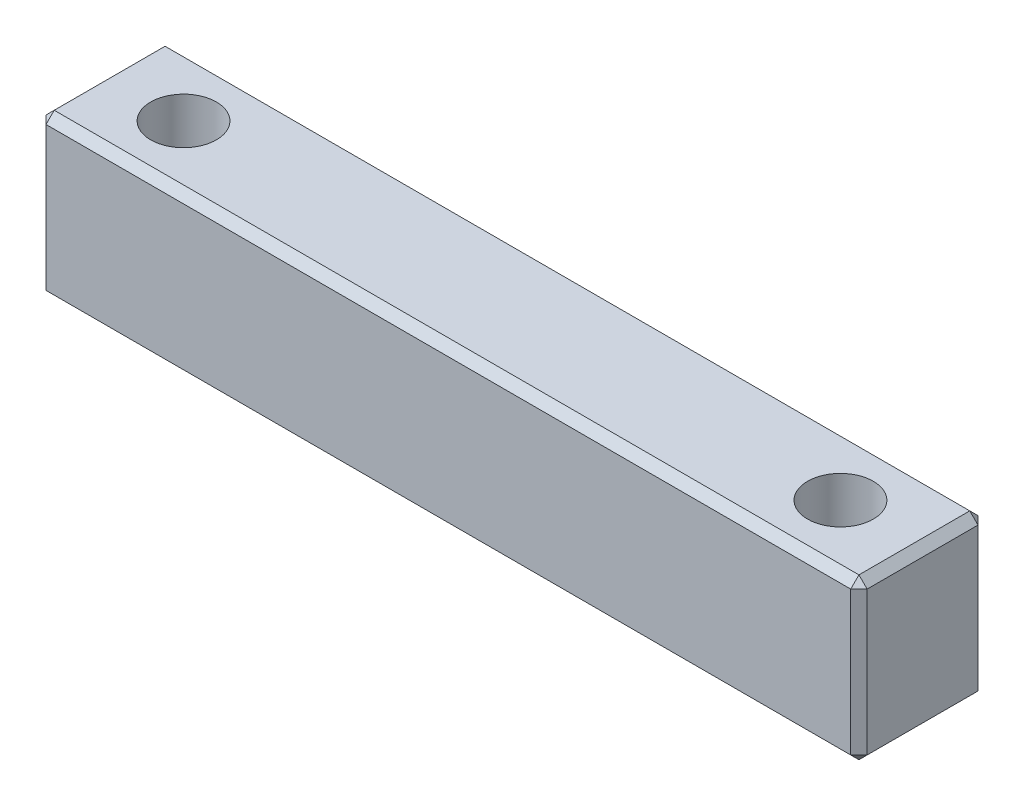
SolidWorks part; units mm, degrees
ref_plane "Front Plane" through (0, 0, 0) normal (0, 0, 1) x (1, 0, 0)
ref_plane "Top Plane" through (0, 0, 0) normal (0, 1, 0) x (1, 0, 0)
ref_plane "Right Plane" through (0, 0, 0) normal (1, 0, 0) x (0, 0, -1)
sketch "Sketch1" plane through (0, 0, 0) normal (1, 0, 0) x (0, 0, -1)
  line L1 (0, 0) -> (7.75, 0)
  line L2 (0, 0) -> (0, 9.75)
  line L3 (0, 9.75) -> (7.75, 9.75)
  line L4 (7.75, 0) -> (7.75, 9.75)
  dimension "D1" = 7.75
  dimension "D2" = 9.75
extrude "Boss-Extrude1" add sketch "Sketch1" along normal blind 50
sketch "Sketch4" plane through (0, 9.75, 0) normal (0, 1, 0) x (1, 0, 0)
  line L0 (0, 3.875) -> (5, 3.875) construction
  line L1 (0, 7.75) -> (0, 0) construction
  line L2 (50, 3.875) -> (45, 3.875) construction
  line L3 (50, 7.75) -> (50, 0) construction
  circle A2 centre (5, 3.875) radius 2
  circle A3 centre (45, 3.875) radius 2
  dimension "D2" = 5
  dimension "D1" = 5
extrude "Cut-Extrude3" cut sketch "Sketch4" against normal up to surface (9.75 mm away) up to face at (25, 0, -3.875)
chamfer "Chamfer1" distance 0.5 angle 45 12 edges at (0, 0, -3.875) (0, 9.75, -3.875) (25, 9.75, 0) (0, 4.875, 0) (25, 0, 0) (25, 0, -7.75) (0, 4.875, -7.75) (25, 9.75, -7.75) (50, 9.75, -3.875) (50, 4.875, -7.75) (50, 0, -3.875) (50, 4.875, 0)
